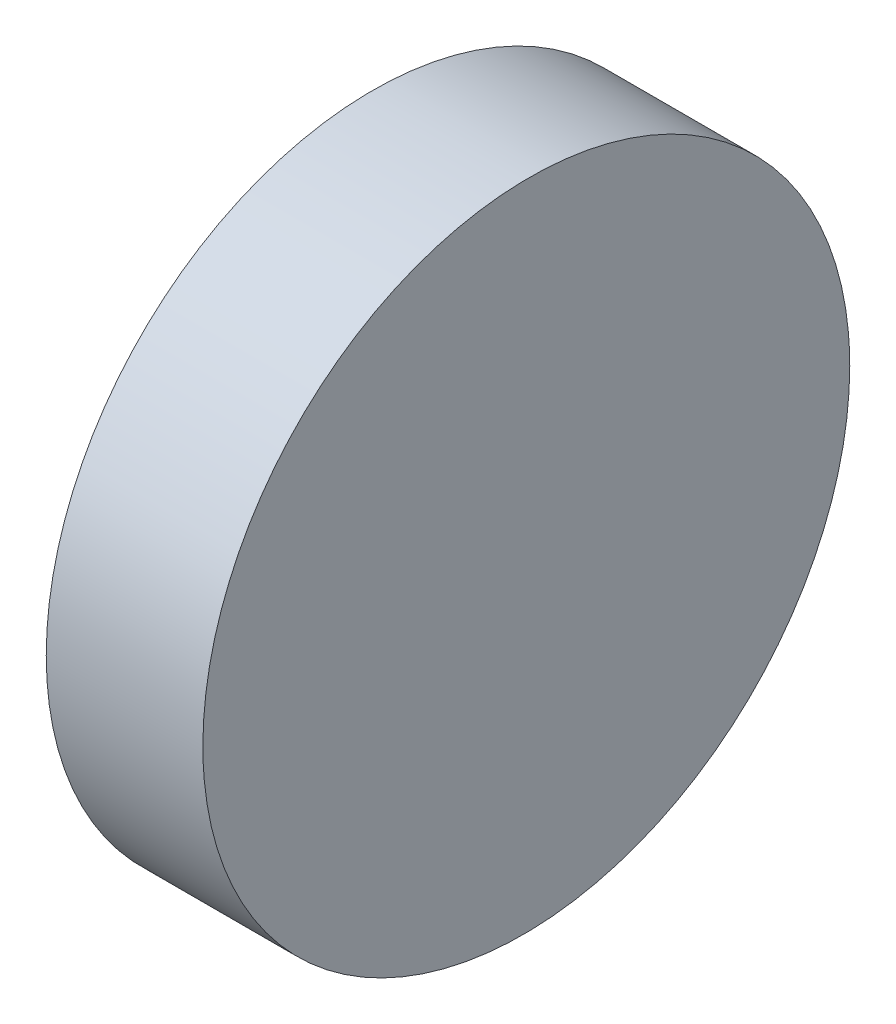
SolidWorks part; units mm, degrees
ref_plane "前视基准面" through (0, 0, 0) normal (0, 0, 1) x (1, 0, 0)
ref_plane "上视基准面" through (0, 0, 0) normal (0, 1, 0) x (1, 0, 0)
ref_plane "右视基准面" through (0, 0, 0) normal (1, 0, 0) x (0, 0, -1)
sketch "草图1" plane through (0, 0, 0) normal (0, 1, 0) x (1, 0, 0)
  line L0 (-12.1202, 0) -> (19.0875, 0) construction
  line L1 (0, 6.25) -> (0, -6.25)
  line L2 (0, -6.25) -> (3, -6.25)
  line L3 (3, -6.25) -> (2.8909, 6.25)
  line L4 (0, 6.25) -> (2.8909, 6.25)
  point P5 (0, 0)
  dimension "D1" = 3
  dimension "D2" = 12.5
  dimension "D3" = 0.5
extrude "凸台-拉伸1" add sketch "草图1" along normal blind 12.5
sketch "草图5" plane through (0, 0, 0) normal (-1, 0, 0) x (0, 0, 1)
  line L0 (0, 0) -> (0, 12.5) construction
  line L1 (-6.25, 12.5) -> (6.25, 12.5) construction
  line L2 (0, 12.5) -> (0.9302, 12.292) construction
  line L3 (-6.25, 6.25) -> (6.25, 6.25) construction
  line L4 (-6.25, 12.5) -> (-6.25, 0) construction
  line L5 (6.25, 12.5) -> (6.25, 0) construction
  line L6 (6.25, 6.25) -> (6.6453, 6.1075) construction
  line L11 (-6.25, 0) -> (6.25, 0)
  line L12 (6.25, 0) -> (6.25, 12.5)
  line L13 (6.25, 12.5) -> (-6.25, 12.5)
  line L14 (-6.25, 12.5) -> (-6.25, 0)
  line L15 (-6.25, 0) -> (6.25, 0)
  line L16 (6.25, 0) -> (6.25, 12.5)
  line L17 (6.25, 12.5) -> (-6.25, 12.5)
  line L18 (-6.25, 12.5) -> (-6.25, 0)
  circle A0 centre (0, 6.25) radius 6.25
  line M5 (-6.25, 0) -> (6.25, 0)
  line M6 (6.25, 0) -> (6.25, 12.5)
  line M7 (6.25, 12.5) -> (-6.25, 12.5)
  line M8 (-6.25, 12.5) -> (-6.25, 0)
  dimension "D1" = 12.5
  dimension "D2" = 0
extrude "切除-拉伸2" cut sketch "草图5" against normal blind 12.5 contours A0 L17 M8 | A0 L18 M5 | A0 L15 M6 | A0 L16 M7
